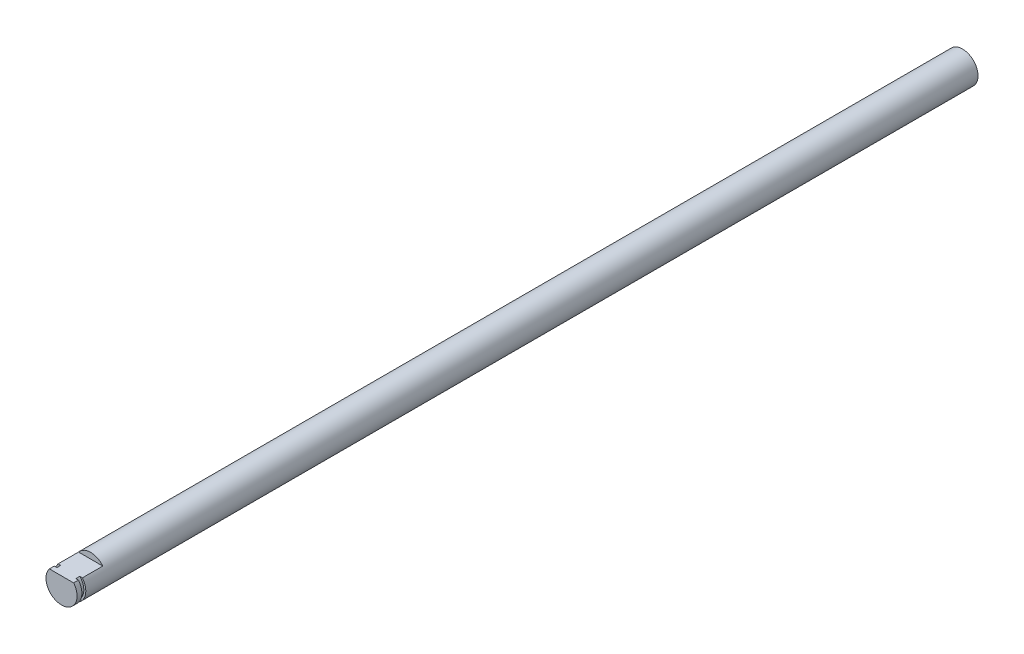
SolidWorks part; units mm, degrees
ref_plane "Front Plane" through (0, 0, 0) normal (0, 0, 1) x (1, 0, 0)
ref_plane "Top Plane" through (0, 0, 0) normal (0, 1, 0) x (1, 0, 0)
ref_plane "Right Plane" through (0, 0, 0) normal (1, 0, 0) x (0, 0, -1)
sketch "Sketch1" plane through (0, 0, 0) normal (0, 0, 1) x (1, 0, 0)
  circle A0 centre (0, 0) radius 4
  dimension "D1" = 8
extrude "Boss-Extrude1" add sketch "Sketch1" along normal blind 325
sketch "Sketch2" plane through (0, 0, 325) normal (0, 0, 1) x (1, 0, 0)
  line L0 (3.1225, 2.5) -> (-3.1225, 2.5)
  circle A1 centre (0, 0) radius 4
  arc A2 (3.1225, 2.5) -> (-3.1225, 2.5) centre (0, 0) ccw
  dimension "D2" = 2.5
  dimension "D1" = 0
extrude "Cut-Extrude1" cut sketch "Sketch2" against normal blind 7.5
ref_plane "Plane1" through (0, 0, 323.75) normal (0, 0, 1) x (1, 0, 0)
sketch "Sketch3" plane through (0, 0, 323.75) normal (0, 0, 1) x (1, 0, 0)
  circle A0 centre (0, 0) radius 4
  circle A1 centre (0, 0) radius 3.5
extrude "Cut-Extrude2" cut sketch "Sketch3" against normal blind 1
sketch "Sketch5" plane through (0, 0, 0) normal (0, 0, -1) x (-1, 0, 0)
  circle A1 centre (0, 0) radius 4
  circle A2 centre (0, 0) radius 4
  dimension "D1" = 0
extrude "Cut-Extrude3" cut sketch "Sketch5" against normal blind 65
sketch "Sketch6" plane through (0, 0, 65) normal (0, 0, -1) x (-1, 0, 0)
  circle A1 centre (0, 0) radius 4
  circle A2 centre (0, 0) radius 4
  dimension "D1" = 0
extrude "Boss-Extrude2" add sketch "Sketch6" along normal blind 13
sketch "Sketch7" plane through (0, 0, 52) normal (0, 0, -1) x (-1, 0, 0)
  circle A1 centre (0, 0) radius 4
  circle A2 centre (0, 0) radius 4
  dimension "D1" = 0
extrude "Boss-Extrude3" add sketch "Sketch7" along normal blind 10
sketch "Sketch8" plane through (0, 0, 42) normal (0, 0, -1) x (-1, 0, 0)
  circle A1 centre (0, 0) radius 4
  circle A2 centre (0, 0) radius 4
  dimension "D1" = 0
extrude "Boss-Extrude4" add sketch "Sketch8" along normal blind 40
sketch "Sketch9" plane through (0, 0, 2) normal (0, 0, -1) x (-1, 0, 0)
  circle A1 centre (0, 0) radius 4
  circle A2 centre (0, 0) radius 4
  dimension "D1" = 0
extrude "Cut-Extrude4" cut sketch "Sketch9" against normal blind 30
sketch "Sketch10" plane through (0, 0, 32) normal (0, 0, -1) x (-1, 0, 0)
  circle A0 centre (0, 0) radius 4 construction
  circle A1 centre (0, 0) radius 4
extrude "Cut-Extrude5" cut sketch "Sketch10" against normal blind 61
